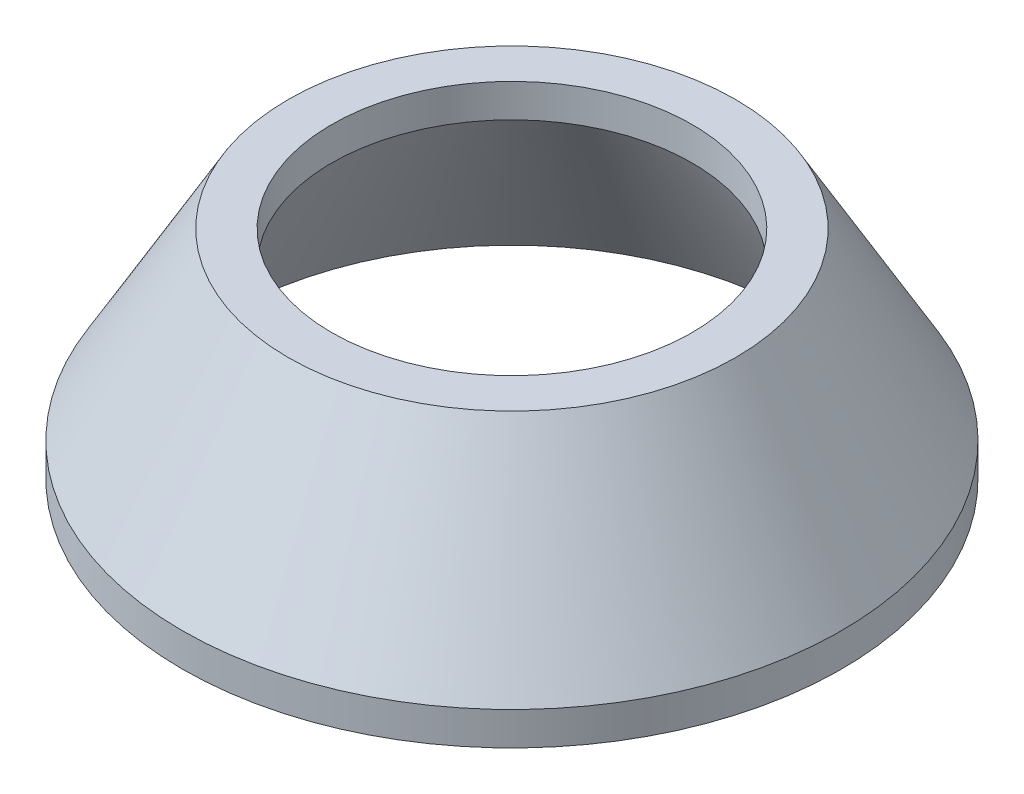
SolidWorks part; units mm, degrees
ref_plane "Front Plane" through (0, 0, 0) normal (0, 0, 1) x (1, 0, 0)
ref_plane "Top Plane" through (0, 0, 0) normal (0, 1, 0) x (1, 0, 0)
ref_plane "Right Plane" through (0, 0, 0) normal (1, 0, 0) x (0, 0, -1)
sketch "Sketch1" plane through (0, 0, 0) normal (0, 0, 1) x (1, 0, 0)
  line L0 (0, 26.383) -> (0, -34.6556) construction
  line L1 (33.25, 40) -> (33.25, 33.8564)
  line L2 (33.25, 33.8564) -> (52.797, 0)
  line L3 (52.797, 0) -> (60.797, 0)
  line L4 (60.797, 6.1436) -> (41.25, 40)
  line L5 (41.25, 40) -> (33.25, 40)
  line L6 (60.797, 0) -> (60.797, 6.1436)
  point P5 (37.25, 40)
  point P9 (56.797, 0)
  dimension "D1" = 10
  dimension "D2" = 74.5
  dimension "D3" = 30
  dimension "D4" = 40
  dimension "D5" = 8
revolve "Revolve1" add sketch "Sketch1" angle 360 about L0
